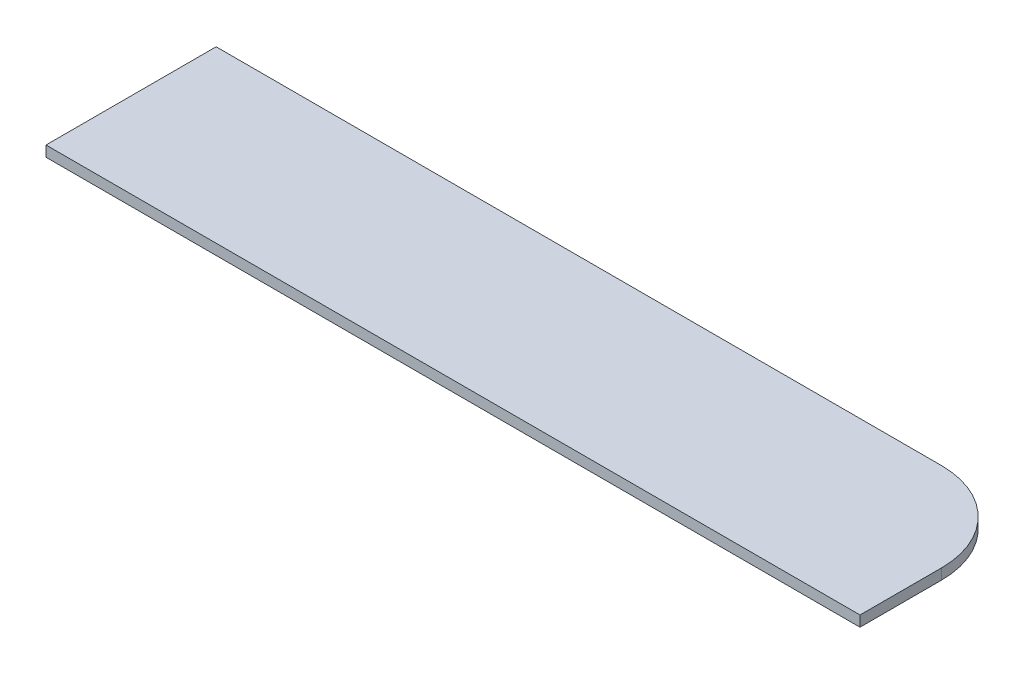
SolidWorks part; units mm, degrees
ref_plane "Front Plane" through (0, 0, 0) normal (0, 0, 1) x (1, 0, 0)
ref_plane "Top Plane" through (0, 0, 0) normal (0, 1, 0) x (1, 0, 0)
ref_plane "Right Plane" through (0, 0, 0) normal (1, 0, 0) x (0, 0, -1)
sketch "Sketch1" plane through (0, 0, 0) normal (0, 1, 0) x (1, 0, 0)
  line L1 (689, -144) -> (-689, -144)
  line L2 (689, -144) -> (689, -6)
  line L3 (539, 144) -> (-689, 144)
  line L4 (-689, -144) -> (-689, 144)
  line L5 (689, -144) -> (-689, 144) construction
  line L6 (689, 144) -> (-689, -144) construction
  arc A0 (539, 144) -> (689, -6) centre (539, -6) cw
  point P0 (0, 0)
  dimension "D3" = 150
  dimension "D1" = 288
  dimension "D2" = 1378
extrude "Boss-Extrude1" add sketch "Sketch1" along normal blind 18
equation "\"H_DSP\"=18"
equation "\"D1@Boss-Extrude1\"=\"H_DSP\""
